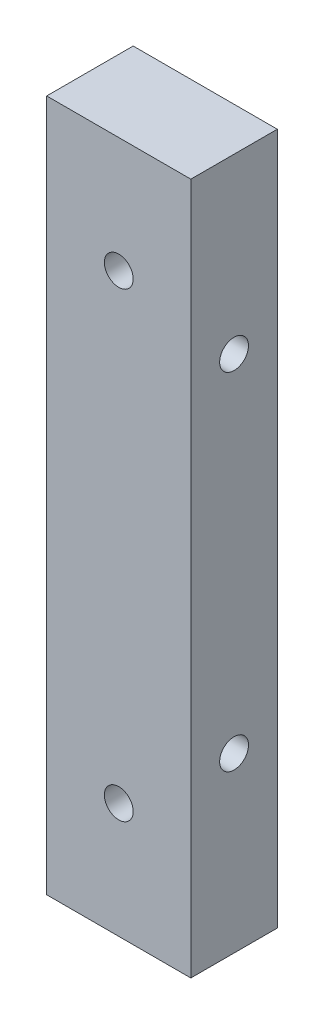
SolidWorks part; units mm, degrees
material "3.3315 (EN-AW 5005)"
ref_plane "Front Plane" through (0, 0, 0) normal (0, 0, 1) x (1, 0, 0)
ref_plane "Top Plane" through (0, 0, 0) normal (0, 1, 0) x (1, 0, 0)
ref_plane "Right Plane" through (0, 0, 0) normal (1, 0, 0) x (0, 0, -1)
sketch "Sketch1" plane through (0, 0, 0) normal (0, 1, 0) x (1, 0, 0)
  line L1 (-12.5, -7.5) -> (12.5, -7.5)
  line L2 (-12.5, -7.5) -> (-12.5, 7.5)
  line L3 (-12.5, 7.5) -> (12.5, 7.5)
  line L4 (12.5, -7.5) -> (12.5, 7.5)
  line L5 (-12.5, -7.5) -> (12.5, 7.5) construction
  line L6 (-12.5, 7.5) -> (12.5, -7.5) construction
  point P0 (0, 0)
  dimension "D1" = 25
  dimension "D2" = 15
extrude "Boss-Extrude1" add sketch "Sketch1" along normal mid plane 120
hole_wizard "M6 Tapped Hole1" positions "Sketch2" profile "Sketch3" tap size "M6" standard "ISO" end condition through all
sketch "Sketch2" plane through (-12.5, 0, 0) normal (-1, 0, 0) x (0, 0, 1)
  point P0 (0, 30)
  point P3 (0, -30)
sketch "Sketch3" plane through (-12.5, 30, 0) normal (0, 1, 0) x (0, 0, 1)
  line L0 (0, 0) -> (0, 25)
  line L1 (0, 25) -> (2.5, 25)
  line L2 (2.5, 25) -> (2.5, 0)
  line L5 (2.5, 0) -> (0, 0)
  line L11 (0, -6.35) -> (0, 107.95) construction
  dimension "Thru Tap Drill Dia." = 5
  dimension "Thru Tap Drill Depth" = 25
cosmetic thread "Hole Thread1" parameters "D2"=6
cosmetic thread "Hole Thread2" parameters "D2"=6
hole_wizard "M6 Tapped Hole2" positions "Sketch4" profile "Sketch5" tap size "M6" standard "ISO" end condition through all
sketch "Sketch4" plane through (0, 0, 7.5) normal (0, 0, 1) x (1, 0, 0)
  point P0 (0, 40)
  point P3 (0, -40)
sketch "Sketch5" plane through (0, 40, 7.5) normal (1, 0, 0) x (0, -1, 0)
  line L0 (0, 0) -> (0, 15)
  line L1 (0, 15) -> (2.5, 15)
  line L2 (2.5, 15) -> (2.5, 0)
  line L5 (2.5, 0) -> (0, 0)
  line L11 (0, -6.35) -> (0, 107.95) construction
  dimension "Thru Tap Drill Dia." = 5
  dimension "Thru Tap Drill Depth" = 15
cosmetic thread "Hole Thread3" parameters "D2"=6
cosmetic thread "Hole Thread4" parameters "D2"=6
